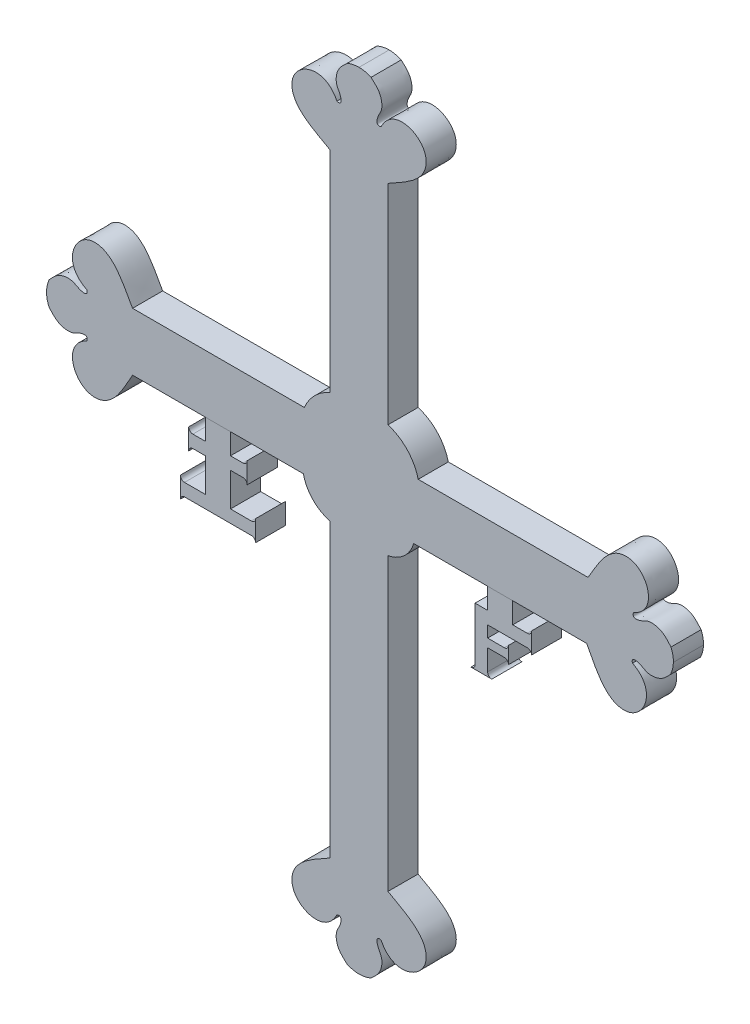
SolidWorks part; units mm, degrees
ref_plane "Alzado" through (0, 0, 0) normal (0, 0, 1) x (1, 0, 0)
ref_plane "Planta" through (0, 0, 0) normal (0, 1, 0) x (1, 0, 0)
ref_plane "Vista lateral" through (0, 0, 0) normal (1, 0, 0) x (0, 0, -1)
sketch "Croquis1" plane through (0, 0, 0) normal (0, 0, 1) x (1, 0, 0)
  line L0 (-363.8339, 123.8944) -> (-30.5006, 123.8944) construction
  line L1 (-250.9984, 164.7424) -> (-250.9984, 114.5106)
  line L2 (-237.1616, 164.7424) -> (-237.1616, 114.7424)
  line L3 (-243.8551, 101.1993) -> (-243.7348, 111.5516) construction
  line L4 (-250.9984, 164.7424) -> (-237.1616, 164.7424) construction
  line L5 (-318.7128, 186.4387) -> (-168.7128, -3.5613) construction
  line L6 (-318.7128, -3.5613) -> (-168.7128, 186.4387) construction
  line L7 (-244.08, 164.7424) -> (-244.08, 185.3129) construction
  line L8 (-189.3337, 107.077) -> (-189.6553, 93.244) construction
  line L9 (-189.4945, 100.1605) -> (-168.9295, 99.6824) construction
  line L10 (-189.6553, 93.244) -> (-231.0126, 93.244)
  line L11 (-189.3337, 107.077) -> (-229.9386, 107.077)
  line L12 (-244.1625, 86.0955) -> (-259.9815, 86.0955) construction
  line L13 (-243.9913, 94.5058) -> (-251.5857, 94.5058) construction
  line L14 (-243.7128, 91.4387) -> (-250.9984, 91.4387) construction
  line L15 (-244.08, 18.135) -> (-244.08, -2.4355) construction
  line L16 (-298.2252, 94.5058) -> (-257.3982, 94.5058)
  line L17 (-298.2252, 101.1993) -> (-180.312, 101.4242) construction
  line L18 (-243.5477, 116.303) -> (-244.1625, 86.0955) construction
  line L19 (-180.312, 108.3426) -> (-287.312, 108.3426) construction
  line L20 (-307.3982, 94.056) -> (-307.3982, 107.8928) construction
  line L21 (-307.3982, 100.9744) -> (-327.9687, 100.9744) construction
  line L22 (-250.9984, 18.135) -> (-237.1616, 18.135) construction
  line L23 (-307.3982, 107.8928) -> (-257.3982, 107.8928) [skipped]
  line L24 (-287.312, 108.3426) -> (-233.812, 108.3426) construction
  line L25 (-233.812, 108.3426) -> (-233.812, 89.9141) construction
  line L26 (-239.2686, 101.3117) -> (-239.2686, 86.8055) construction
  line L27 (-298.2252, 101.4242) -> (-318.7958, 101.4242) construction
  line L28 (-298.2252, 108.3426) -> (-298.2252, 94.5058) construction
  line L29 (-298.2252, 108.3426) -> (-257.1665, 108.3426)
  line L30 (-180.312, 108.3426) -> (-180.312, 94.5058) construction
  line L31 (-180.312, 101.4242) -> (-159.7415, 101.4242) construction
  line L32 (-180.312, 94.5058) -> (-230.312, 94.5058) [skipped]
  line L33 (-250.9984, 18.135) -> (-250.9984, 87.888)
  line L34 (-236.7119, 37.6562) -> (-250.5486, 37.6562) construction
  line L35 (-243.6302, 37.6562) -> (-243.6302, 17.0857) construction
  line L36 (-250.5486, 37.6562) -> (-250.5486, 87.6562) [skipped]
  line L37 (-237.1616, 18.135) -> (-237.1616, 87.6562)
  arc A0 (-257.1665, 108.3426) -> (-250.9984, 114.5106) centre (-246.4666, 103.8108) cw
  arc A1 (-237.1616, 114.7424) -> (-229.9386, 107.077) centre (-240.2666, 104.5808) cw
  arc A2 (-257.3982, 94.5058) -> (-250.9984, 87.888) centre (-248.8277, 96.3905) ccw
  arc A3 (-237.1616, 87.6562) -> (-231.0126, 93.244) centre (-238.6457, 95.4666) ccw
  spline S0 degree 3 poles (-250.9984, 164.7424) (-253.872, 166.4695) (-260.1017, 169.0667) (-260.254, 178.5935) (-252.1891, 181.4893) (-249.3689, 175.6583) knots 0 0 0 0 0.445418 0.535608 1 1 1 1
  spline S1 degree 3 poles (-237.1616, 164.7424) (-234.288, 166.4695) (-228.0583, 169.0667) (-227.906, 178.5935) (-235.9709, 181.4893) (-238.7911, 175.6583) knots 0 0 0 0 0.445418 0.535608 1 1 1 1
  spline S2 degree 3 poles (-249.3689, 175.6583) (-248.1254, 175.2612) (-248.3902, 177.3738) (-249.6384, 179.0551) (-249.5743, 181.2866) (-248.5877, 183.2614) (-247.5015, 184.1496) (-246.9598, 184.6861) knots 0 0 0 0 0.226165 0.394336 0.620843 0.785939 1 1 1 1
  spline S3 degree 2 poles (-246.9598, 184.6861) (-245.5194, 185.3179) (-244.08, 185.3129) knots 0 0 0 0.504568 0.504568 0.504568
  spline S4 degree 2 poles (-241.2002, 184.6861) (-242.6406, 185.3179) (-244.08, 185.3129) knots 0 0 0 0.504568 0.504568 0.504568
  spline S5 degree 3 poles (-238.7911, 175.6583) (-240.0346, 175.2612) (-239.7698, 177.3738) (-238.5216, 179.0551) (-238.5857, 181.2866) (-239.5724, 183.2614) (-240.6585, 184.1496) (-241.2002, 184.6861) knots 0 0 0 0 0.226165 0.394336 0.620843 0.785939 1 1 1 1
  spline S6 degree 3 poles (-189.3337, 107.077) (-187.5402, 109.9097) (-184.799, 116.0774) (-175.2712, 116.0082) (-172.5636, 107.8782) (-178.4586, 105.1942) knots 0 0 0 0 0.445418 0.535608 1 1 1 1
  spline S7 degree 3 poles (-189.6553, 93.244) (-187.9954, 90.331) (-185.5437, 84.0426) (-176.023, 83.669) (-172.9405, 91.6644) (-178.7044, 94.6194) knots 0 0 0 0 0.445418 0.535608 1 1 1 1
  spline S8 degree 3 poles (-178.4586, 105.1942) (-178.8844, 103.9604) (-176.7663, 104.176) (-175.0564, 105.3848) (-172.827, 105.2688) (-170.8757, 104.2365) (-170.013, 103.1301) (-169.4892, 102.576) knots 0 0 0 0 0.226165 0.394336 0.620843 0.785939 1 1 1 1
  spline S9 degree 2 poles (-169.4892, 102.576) (-168.891, 101.1213) (-168.9295, 99.6824) knots 0 0 0 0.504568 0.504568 0.504568
  spline S10 degree 2 poles (-169.6231, 96.818) (-168.9579, 98.2433) (-168.9295, 99.6824) knots 0 0 0 0.504568 0.504568 0.504568
  spline S11 degree 3 poles (-178.7044, 94.6194) (-179.0725, 95.8717) (-176.9667, 95.5579) (-175.3148, 94.2709) (-173.0824, 94.2832) (-171.0852, 95.2237) (-170.172, 96.2889) (-169.6231, 96.818) knots 0 0 0 0 0.226165 0.394336 0.620843 0.785939 1 1 1 1
  spline S12 degree 3 poles (-238.7911, 7.219) (-240.0346, 7.6161) (-239.7698, 5.5036) (-238.5216, 3.8223) (-238.5857, 1.5907) (-239.5724, -0.384) (-240.6585, -1.2723) (-241.2002, -1.8087) knots 0 0 0 0 0.226165 0.394336 0.620843 0.785939 1 1 1 1
  spline S13 degree 2 poles (-241.2002, -1.8087) (-242.6406, -2.4406) (-244.08, -2.4355) knots 0 0 0 0.504568 0.504568 0.504568
  spline S14 degree 2 poles (-246.9598, -1.8087) (-245.5194, -2.4406) (-244.08, -2.4355) knots 0 0 0 0.504568 0.504568 0.504568
  spline S15 degree 3 poles (-249.3689, 7.219) (-248.1254, 7.6161) (-248.3902, 5.5036) (-249.6384, 3.8223) (-249.5743, 1.5907) (-248.5877, -0.384) (-247.5015, -1.2723) (-246.9598, -1.8087) knots 0 0 0 0 0.226165 0.394336 0.620843 0.785939 1 1 1 1
  spline S16 degree 3 poles (-237.1616, 18.135) (-234.288, 16.4078) (-228.0583, 13.8107) (-227.906, 4.2839) (-235.9709, 1.3881) (-238.7911, 7.219) knots 0 0 0 0 0.445418 0.535608 1 1 1 1
  spline S17 degree 3 poles (-250.9984, 18.135) (-253.872, 16.4078) (-260.1017, 13.8107) (-260.254, 4.2839) (-252.1891, 1.3881) (-249.3689, 7.219) knots 0 0 0 0 0.445418 0.535608 1 1 1 1
  spline S18 degree 3 poles (-309.1412, 96.1353) (-308.7441, 97.3787) (-310.8566, 97.114) (-312.538, 95.8658) (-314.7695, 95.9299) (-316.7442, 96.9165) (-317.6325, 98.0026) (-318.1689, 98.5444) knots 0 0 0 0 0.226165 0.394336 0.620843 0.785939 1 1 1 1
  spline S19 degree 2 poles (-318.1689, 98.5444) (-318.8008, 99.9848) (-318.7958, 101.4242) knots 0 0 0 0.504568 0.504568 0.504568
  spline S20 degree 2 poles (-318.1689, 104.304) (-318.8008, 102.8636) (-318.7958, 101.4242) knots 0 0 0 0.504568 0.504568 0.504568
  spline S21 degree 3 poles (-309.1412, 106.713) (-308.7441, 105.4696) (-310.8566, 105.7344) (-312.538, 106.9826) (-314.7695, 106.9185) (-316.7442, 105.9318) (-317.6325, 104.8457) (-318.1689, 104.304) knots 0 0 0 0 0.226165 0.394336 0.620843 0.785939 1 1 1 1
  spline S22 degree 3 poles (-298.2252, 94.5058) (-299.9524, 91.6322) (-302.5496, 85.4025) (-312.0764, 85.2502) (-314.9721, 93.3151) (-309.1412, 96.1353) knots 0 0 0 0 0.445418 0.535608 1 1 1 1
  spline S23 degree 3 poles (-298.2252, 108.3426) (-299.9524, 111.2162) (-302.5496, 117.4459) (-312.0764, 117.5982) (-314.9721, 109.5332) (-309.1412, 106.713) knots 0 0 0 0 0.445418 0.535608 1 1 1 1
  point P0 (-243.7128, 91.4387)
  point P139 (-243.8551, 101.1993)
  dimension "D1" = 150
  dimension "D2" = 190
  dimension "D3" = 41.0588
  dimension "D4" = 4
  dimension "D6" = 0.5
extrude "Saliente-Extruir1" add sketch "Croquis1" along normal blind 7.2
sketch "Croquis2" plane through (0, 0, 7.2) normal (0, 0, 1) x (1, 0, 0)
  line L0 (-298.2252, 94.5058) -> (-257.3982, 94.5058) construction
  line L1 (-283.8117, 89.5058) -> (-283.8117, 90.5058) construction
  line L2 (-280.8117, 94.5058) -> (-280.8117, 89.5058)
  line L3 (-280.8117, 89.5058) -> (-283.8117, 89.5058)
  line L4 (-284.8117, 90.5058) -> (-284.8117, 85.5058)
  line L5 (-283.8117, 86.5058) -> (-280.8117, 86.5058)
  line L6 (-280.8117, 86.5058) -> (-280.8117, 78.5058)
  line L7 (-280.8117, 78.5058) -> (-285.8117, 78.5058)
  line L8 (-286.8117, 79.5058) -> (-286.8117, 74.5058)
  line L9 (-285.8117, 75.5058) -> (-269.8117, 75.5058)
  line L10 (-216.3339, 75.5058) -> (-217.3339, 75.5058) construction
  line L11 (-269.8117, 78.5058) -> (-274.8117, 78.5058)
  line L12 (-274.8117, 78.5058) -> (-274.8117, 86.5058)
  line L13 (-274.8117, 86.5058) -> (-271.8117, 86.5058)
  line L14 (-270.8117, 90.5058) -> (-270.8117, 85.5058)
  line L15 (-271.8117, 89.5058) -> (-274.8117, 89.5058)
  line L16 (-274.8117, 89.5058) -> (-274.8117, 94.5058)
  line L17 (-231.0126, 93.244) -> (-189.6553, 93.244) construction
  line L18 (-210.3339, 93.244) -> (-213.3339, 93.244)
  line L19 (-213.3339, 93.244) -> (-213.3339, 88.244)
  line L20 (-213.3339, 88.244) -> (-216.3339, 88.244)
  line L21 (-216.3339, 88.244) -> (-216.3339, 75.5058)
  line L22 (-208.3339, 83.5058) -> (-208.3339, 79.5058)
  line L23 (-213.3339, 75.5058) -> (-213.3339, 80.5058)
  line L24 (-213.3339, 80.5058) -> (-209.3339, 80.5058)
  line L25 (-209.3339, 82.5058) -> (-209.3339, 83.5058) construction
  line L26 (-209.3339, 83.5058) -> (-208.3339, 83.5058) construction
  line L27 (-213.3339, 83.5058) -> (-213.3339, 85.2458)
  line L28 (-213.3339, 85.2458) -> (-203.8348, 85.2458)
  line L30 (-203.8348, 88.244) -> (-207.3348, 88.244)
  line L31 (-207.3348, 88.244) -> (-207.3348, 93.244)
  line L32 (-207.3348, 93.244) -> (-213.3339, 93.244)
  line L33 (-280.8117, 94.5058) -> (-274.8117, 94.5058)
  line L34 (-283.8117, 90.5058) -> (-284.8117, 90.5058) construction
  line L35 (-284.8117, 90.5058) -> (-284.8117, 85.5058) construction
  line L36 (-284.8117, 85.5058) -> (-283.8117, 85.5058) construction
  line L37 (-283.8117, 85.5058) -> (-283.8117, 86.5058) construction
  line L38 (-285.8117, 78.5058) -> (-285.8117, 79.5058) construction
  line L39 (-285.8117, 79.5058) -> (-286.8117, 79.5058) construction
  line L40 (-286.8117, 79.5058) -> (-286.8117, 74.5058) construction
  line L41 (-286.8117, 74.5058) -> (-285.8117, 74.5058) construction
  line L42 (-285.8117, 74.5058) -> (-285.8117, 75.5058) construction
  line L43 (-271.8117, 89.5058) -> (-271.8117, 90.5058) construction
  line L44 (-271.8117, 90.5058) -> (-270.8117, 90.5058) construction
  line L45 (-270.8117, 90.5058) -> (-270.8117, 85.5058) construction
  line L46 (-270.8117, 85.5058) -> (-271.8117, 85.5058) construction
  line L47 (-271.8117, 85.5058) -> (-271.8117, 86.5058) construction
  line L48 (-269.8117, 78.5058) -> (-269.8117, 79.5058) construction
  line L49 (-269.8117, 79.5058) -> (-268.8117, 79.5058) construction
  line L50 (-268.8117, 79.5058) -> (-268.8117, 74.5058) construction
  line L51 (-268.8117, 74.5058) -> (-269.8117, 74.5058) construction
  line L52 (-269.8117, 74.5058) -> (-269.8117, 75.5058) construction
  line L53 (-268.8117, 79.5058) -> (-268.8117, 74.5058)
  line L54 (-217.3339, 75.5058) -> (-217.3339, 74.5058) construction
  line L55 (-217.3339, 74.5058) -> (-212.3339, 74.5058) construction
  line L56 (-212.3339, 74.5058) -> (-212.3339, 75.5058) construction
  line L57 (-212.3339, 75.5058) -> (-213.3339, 75.5058) construction
  line L58 (-217.3339, 74.5058) -> (-212.3339, 74.5058)
  line L59 (-209.3339, 82.5058) -> (-213.3339, 82.5058)
  line L60 (-213.3339, 82.5058) -> (-213.3339, 83.5058)
  line L61 (-208.3339, 83.5058) -> (-208.3339, 79.5058) construction
  line L62 (-208.3339, 79.5058) -> (-209.3339, 79.5058) construction
  line L63 (-209.3339, 79.5058) -> (-209.3339, 80.5058) construction
  line L64 (-203.8348, 88.244) -> (-203.8348, 89.2449) construction
  line L65 (-203.8348, 89.2449) -> (-202.8339, 89.2449) construction
  line L66 (-202.8339, 89.2449) -> (-202.8339, 84.2449) construction
  line L67 (-202.8339, 84.2449) -> (-203.8348, 84.2449) construction
  line L68 (-203.8348, 84.2449) -> (-203.8348, 85.2458) construction
  line L69 (-202.8339, 89.2449) -> (-202.8339, 84.2449)
  arc A0 (-284.8117, 85.5058) -> (-283.8117, 86.5058) centre (-283.8117, 85.5058) cw
  arc A1 (-283.8117, 89.5058) -> (-284.8117, 90.5058) centre (-283.8117, 90.5058) cw
  arc A2 (-285.8117, 78.5058) -> (-286.8117, 79.5058) centre (-285.8117, 79.5058) cw
  arc A3 (-285.8117, 75.5058) -> (-286.8117, 74.5058) centre (-285.8117, 74.5058) ccw
  arc A4 (-271.8117, 89.5058) -> (-270.8117, 90.5058) centre (-271.8117, 90.5058) ccw
  arc A5 (-271.8117, 86.5058) -> (-270.8117, 85.5058) centre (-271.8117, 85.5058) cw
  arc A6 (-269.8117, 75.5058) -> (-268.8117, 74.5058) centre (-269.8117, 74.5058) cw
  arc A7 (-269.8117, 78.5058) -> (-268.8117, 79.5058) centre (-269.8117, 79.5058) ccw
  arc A8 (-216.3339, 75.5058) -> (-217.3339, 74.5058) centre (-217.3339, 75.5058) cw
  arc A9 (-213.3339, 75.5058) -> (-212.3339, 74.5058) centre (-212.3339, 75.5058) ccw
  arc A10 (-209.3339, 80.5058) -> (-208.3339, 79.5058) centre (-209.3339, 79.5058) cw
  arc A11 (-209.3339, 82.5058) -> (-208.3339, 83.5058) centre (-209.3339, 83.5058) ccw
  arc A12 (-203.8348, 88.244) -> (-202.8339, 89.2449) centre (-203.8348, 89.2449) ccw
  arc A13 (-203.8348, 85.2458) -> (-202.8339, 84.2449) centre (-203.8348, 84.2449) cw
  line M26 (-298.2252, 94.5058) -> (-257.3982, 94.5058)
extrude "Saliente-Extruir2" add sketch "Croquis2" against normal up to vertex (7.2 mm away) separate body contours A7 L11 L12 L13 A5 L14 A4 L15 L16 L2 L3 A1 L4 A0 L5 L6 L7 A2 L8 A3 L9 A6 L53 M26 | L19 L20 L21 A8 L58 A9 L23 L24 A10 L22 A11 L59 L60 L27 L28 A13 L69 A12 L30 L31 L32
